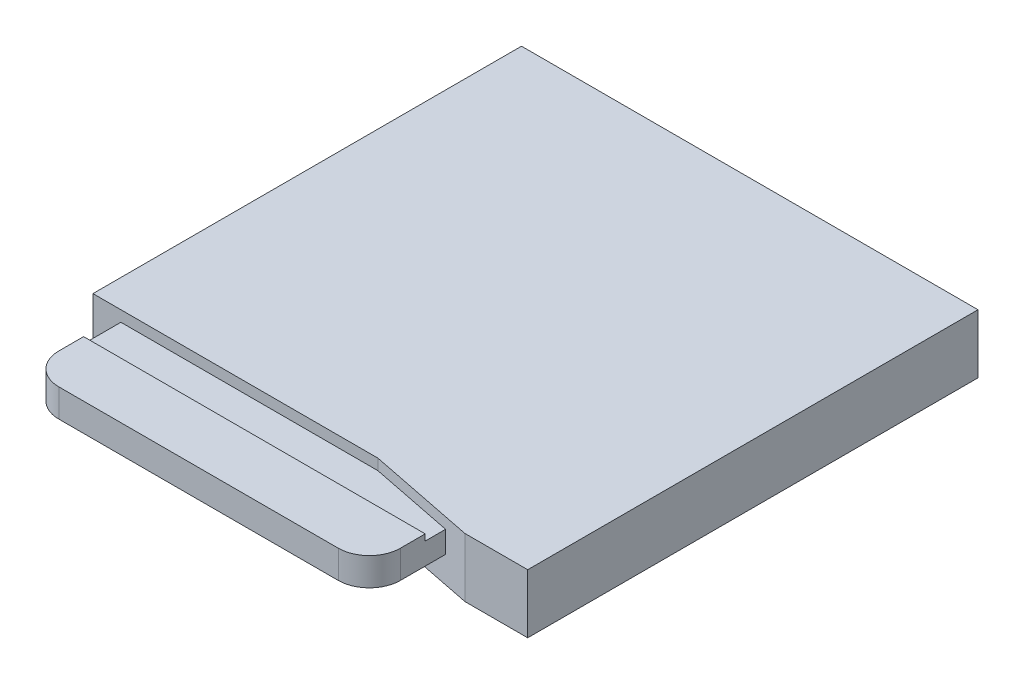
SolidWorks part; units mm, degrees
ref_plane "Front Plane" through (0, 0, 0) normal (0, 0, 1) x (1, 0, 0)
ref_plane "Top Plane" through (0, 0, 0) normal (0, 1, 0) x (1, 0, 0)
ref_plane "Right Plane" through (0, 0, 0) normal (1, 0, 0) x (0, 0, -1)
sketch "Sketch1" plane through (0, 0, 0) normal (0, 1, 0) x (1, 0, 0)
  line L1 (-7.35, -7.25) -> (7.35, -7.25)
  line L2 (-7.35, -7.25) -> (-7.35, 7.25)
  line L3 (-7.35, 7.25) -> (7.35, 7.25)
  line L4 (7.35, -7.25) -> (7.35, 7.25)
  line L5 (-7.35, -7.25) -> (7.35, 7.25) construction
  line L6 (-7.35, 7.25) -> (7.35, -7.25) construction
  point P0 (0, 0)
  dimension "D1" = 14.5
  dimension "D2" = 14.7
extrude "Boss-Extrude1" add sketch "Sketch1" along normal blind 1.9
sketch "Sketch2" plane through (0, 1.9, 0) normal (0, 1, 0) x (1, 0, 0)
  line L0 (-7.35, -6.55) -> (1.8249, -6.55)
  line L1 (-7.35, 7.25) -> (-7.35, -7.25) construction
  line L2 (1.8249, -6.55) -> (5.3285, -7.25)
  line L3 (-7.35, -7.25) -> (7.35, -7.25) construction
  line L4 (7.35, 7.25) -> (-7.35, 7.25) construction
  dimension "D1" = 13.8
extrude "Cut-Extrude1" cut sketch "Sketch2" against normal blind 1.9 and the other way through all flip side to cut
sketch "Sketch3" plane through (0, 0, 6.55) normal (0, 0, 1) x (1, 0, 0)
  line L1 (-6.45, 1.55) -> (4.55, 1.55)
  line L2 (-6.45, 1.55) -> (-6.45, 0.85)
  line L3 (-6.45, 0.85) -> (4.55, 0.85)
  line L4 (4.55, 1.55) -> (4.55, 0.85)
  line L5 (0, 1.9) -> (0, 48.4827) construction
  line L6 (7.35, 1.9) -> (-7.35, 1.9) construction
  line L7 (-0.95, 1.55) -> (-0.95, 0.85) construction
  line L8 (1.8249, 0) -> (-7.35, 0) construction
  point P10 (0, 1.9)
  dimension "D1" = 0.7
  dimension "D2" = 11
  dimension "D3" = 0.85
  dimension "D4" = 0.95
extrude "Boss-Extrude2" add sketch "Sketch3" along normal blind 3
sketch "Sketch4" plane through (0, 1.55, 0) normal (0, 1, 0) x (1, 0, 0)
  line L0 (4.55, -9.55) -> (4.55, -7.0945) construction
  line L1 (-6.45, -9.55) -> (4.55, -9.55)
  line L2 (-6.45, -9.55) -> (-6.45, -7.75)
  line L3 (-6.45, -7.75) -> (4.55, -7.75)
  line L4 (4.55, -9.55) -> (4.55, -7.75)
  dimension "D1" = 1.8
extrude "Boss-Extrude3" add sketch "Sketch4" along normal blind 0.2
fillet "Fillet1" radius 1 2 edges at (-6.45, 1.3, 9.55) (4.55, 1.3, 9.55)
sketch "Sketch5" plane through (0, 0, 0) normal (0, -1, 0) x (1, 0, 0)
  line L0 (0, -7.25) -> (0, 10.8932) construction
  line L1 (7.35, -7.25) -> (-7.35, -7.25) construction
  line L3 (5.3285, 7.25) -> (7.35, 7.25) construction
  circle A0 centre (-4.95, 3.25) radius 0.4
  circle A1 centre (3.05, 3.25) radius 0.4
  point P11 (5.964, 7.25)
  point P12 (0, 0)
  dimension "D1" = 0.8
  dimension "D2" = 4.95
  dimension "D3" = 3.05
  dimension "D4" = 4
extrude "Boss-Extrude4" add sketch "Sketch5" along normal blind 0.55
fillet "Fillet2" radius 0.1 2 edges at (3.05, -0.55, 2.85) (-4.95, -0.55, 2.85)
